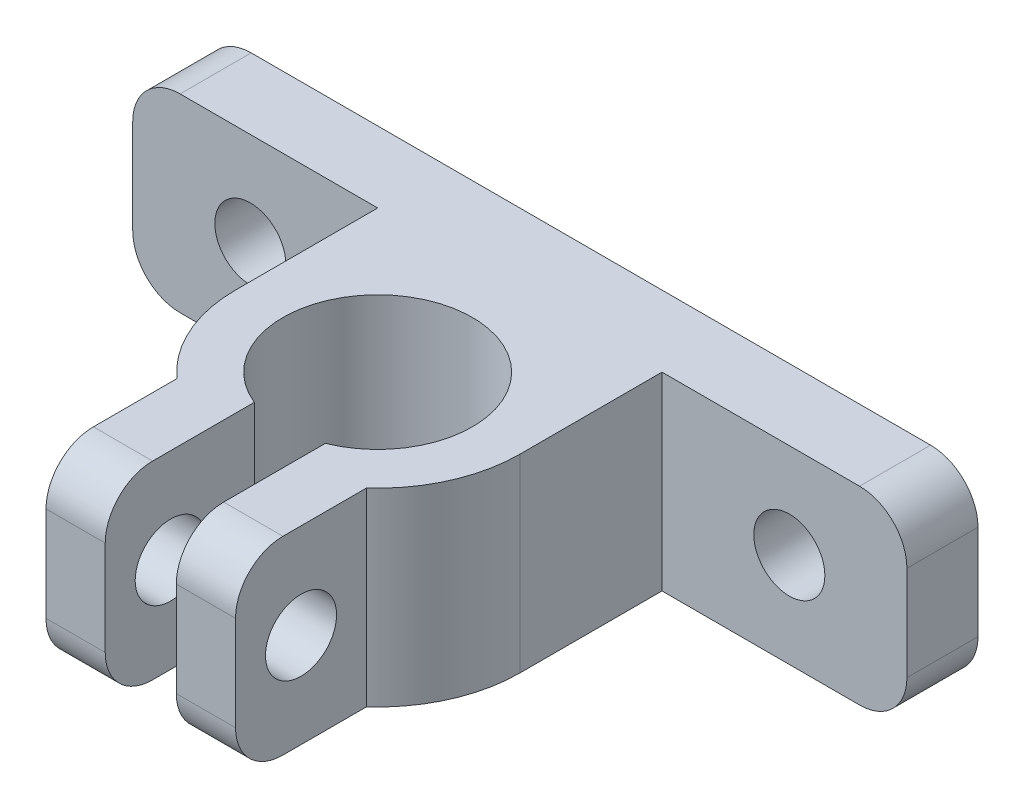
SolidWorks part; units mm, degrees
ref_plane "前视基准面" through (0, 0, 0) normal (0, 0, 1) x (1, 0, 0)
ref_plane "上视基准面" through (0, 0, 0) normal (0, 1, 0) x (1, 0, 0)
ref_plane "右视基准面" through (0, 0, 0) normal (1, 0, 0) x (0, 0, -1)
sketch "草图1" plane through (0, 0, 0) normal (0, 0, 1) x (1, 0, 0)
  line L0 (12.612, 26.3586) -> (-20.0654, 26.3586) construction
  line L2 (-20.0654, 30.3586) -> (12.612, 30.3586)
  line L3 (-20.0654, 30.3586) -> (-20.0654, 22.3586)
  line L4 (-20.0654, 22.3586) -> (12.612, 22.3586)
  line L5 (12.612, 30.3586) -> (12.612, 22.3586)
  line L6 (-20.0654, 30.3586) -> (12.612, 22.3586) construction
  line L7 (-20.0654, 22.3586) -> (12.612, 30.3586) construction
  point P4 (-3.7267, 26.3586)
extrude "凸台-拉伸1" add sketch "草图1" against normal blind 3
sketch "草图2" plane through (0, 0, 0) normal (0, 0, 1) x (1, 0, 0)
  line L0 (-3.7267, 30.3586) -> (-3.7267, 22.3586) construction
  line L3 (12.612, 30.3586) -> (-20.0654, 30.3586) construction
  line L4 (-20.0654, 22.3586) -> (12.612, 22.3586) construction
  line L5 (-3.7267, 26.3586) -> (7.6483, 26.3586) construction
  line L6 (-3.7267, 26.3586) -> (-15.1017, 26.3586) construction
  circle A2 centre (-15.1017, 26.3586) radius 1.5
  circle A3 centre (7.6483, 26.3586) radius 1.5
extrude "切除-拉伸1" cut sketch "草图2" against normal through all
sketch "草图3" plane through (0, 22.3586, 0) normal (0, -1, 0) x (1, 0, 0)
  line L0 (-20.0654, 0) -> (12.612, 0) construction
  line L1 (-3.7267, 0) -> (-3.7267, 6) construction
  circle A0 centre (-3.7267, 6) radius 6
  point P0 (-3.7267, 0)
extrude "凸台-拉伸2" add sketch "草图3" against normal up to surface (8 mm away) separate body up to face at (-3.7267, 30.3586, -1.5)
sketch "草图4" plane through (0, 22.3586, 0) normal (0, -1, 0) x (1, 0, 0)
  circle A0 centre (-3.7267, 6) radius 4
extrude "切除-拉伸2" cut sketch "草图4" against normal through all
sketch "草图5" plane through (0, 22.3586, 0) normal (0, -1, 0) x (1, 0, 0)
  line L0 (-9.7267, 6) -> (-9.7267, 0)
  line L1 (-20.0654, 0) -> (12.612, 0) construction
  line L2 (-9.7267, 0) -> (-3.7267, 0)
  line L3 (-3.7267, 0) -> (-9.7267, 6)
  line L4 (-3.7267, 0) -> (2.2733, 6)
  line L5 (2.2733, 6) -> (2.2733, 0)
  line L6 (2.2733, 0) -> (-3.7267, 0)
  circle A0 centre (-3.7267, 6) radius 6 construction
extrude "凸台-拉伸3" add sketch "草图5" against normal up to surface (8 mm away) contours L3 L0 L2 | L4 L5 L6 up to face at (-3.7267, 30.3586, 2)
sketch "草图6" plane through (0, 22.3586, 0) normal (0, -1, 0) x (1, 0, 0)
  line L0 (-3.7267, 10) -> (4.2733, 10) construction
  line L2 (0.2733, 10) -> (-7.7267, 10)
  line L3 (0.2733, 10) -> (0.2733, 16)
  line L4 (0.2733, 16) -> (-7.7267, 16)
  line L5 (-7.7267, 10) -> (-7.7267, 16)
  circle A0 centre (-3.7267, 6) radius 4 construction
extrude "凸台-拉伸4" add sketch "草图6" against normal up to surface (8 mm away) up to face at (-3.7267, 30.3586, 1.5)
sketch "草图8" plane through (0, 22.3586, 0) normal (0, -1, 0) x (1, 0, 0)
  line L0 (0.2733, 6) -> (-7.7267, 6) construction
  line L2 (-2.2267, 6) -> (-5.2267, 6)
  line L3 (-2.2267, 6) -> (-2.2267, 16.4666)
  line L4 (-2.2267, 16.4666) -> (-5.2267, 16.4666)
  line L5 (-5.2267, 6) -> (-5.2267, 16.4666)
  circle A1 centre (-3.7267, 6) radius 4 construction
  point P8 (-3.7267, 6)
  point P9 (-3.7267, 6)
extrude "切除-拉伸5" cut sketch "草图8" against normal through all
sketch "草图9" plane through (0.2733, 0, 0) normal (1, 0, 0) x (0, 0, -1)
  line L0 (-13.2361, 30.3586) -> (-13.2361, 24.9373) construction
  line L1 (-10.4721, 30.3586) -> (-16, 30.3586) construction
  line L2 (-16, 26.3586) -> (-10.4721, 26.3586) construction
  line L3 (-16, 30.3586) -> (-16, 22.3586) construction
  line L4 (-10.4721, 22.3586) -> (-10.4721, 30.3586) construction
  circle A0 centre (-13.2361, 26.3586) radius 1.5
extrude "切除-拉伸6" cut sketch "草图9" against normal through all
fillet "圆角1" radius 2 4 edges at (12.612, 22.3586, -1.5) (12.612, 30.3586, -1.5) (-20.0654, 22.3586, -1.5) (-20.0654, 30.3586, -1.5)
fillet "圆角2" radius 2 4 edges at (-6.4767, 30.3586, 16) (-6.4767, 22.3586, 16) (-0.9767, 22.3586, 16) (-0.9767, 30.3586, 16)
